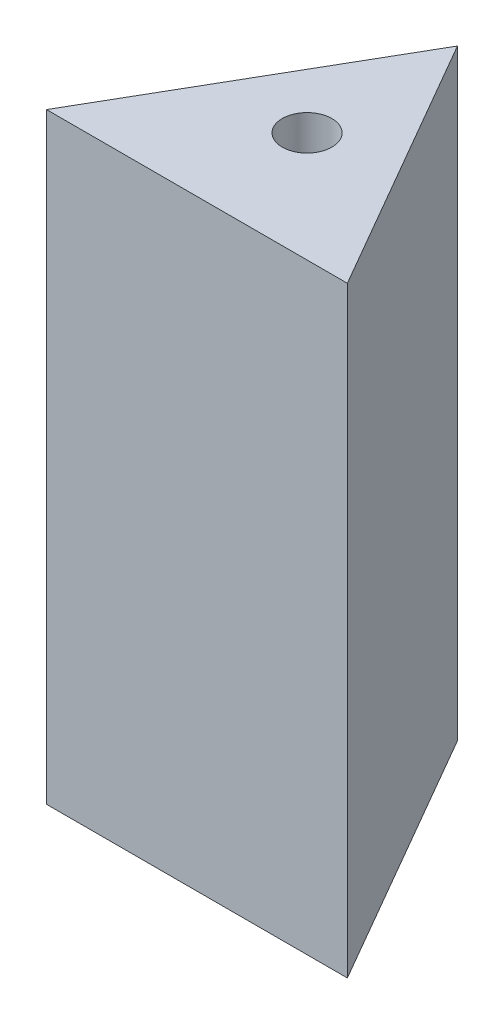
SolidWorks part; units mm, degrees
ref_plane "前视基准面" through (0, 0, 0) normal (0, 0, 1) x (1, 0, 0)
ref_plane "上视基准面" through (0, 0, 0) normal (0, 1, 0) x (1, 0, 0)
ref_plane "右视基准面" through (0, 0, 0) normal (1, 0, 0) x (0, 0, -1)
sketch "草图1" plane through (0, 0, 0) normal (0, 1, 0) x (1, 0, 0)
  line L0 (0, 0) -> (20, 0)
  line L1 (10, 17.3205) -> (20, 0)
  line L2 (0, 0) -> (10, 17.3205)
  line L3 (10, 17.3205) -> (10, 7.3205)
extrude "凸台-拉伸1" add sketch "草图1" along normal blind 40
sketch "草图5" plane through (0, 0, 0) normal (0, -1, 0) x (1, 0, 0)
  line L0 (10, -17.3205) -> (10, -7.3205)
hole_wizard "M4 螺纹孔1" positions "草图6" profile "草图7" tap size "M4" standard "GB"
sketch "草图6" plane through (0, 0, 0) normal (0, -1, 0) x (-1, 0, 0)
  point P0 (-10, 7.3205)
sketch "草图7" plane through (10, 0, -7.3205) normal (1, 0, 0) x (0, 0, -1)
  line L0 (0, 0) -> (0, 11.0914)
  line L1 (0, 11.0914) -> (1.65, 10.1)
  line L2 (1.65, 10.1) -> (1.65, 0)
  line L5 (1.65, 0) -> (0, 0)
  line L10 (0, 11.0914) -> (-1.65, 10.1) construction
  line L11 (0, -6.35) -> (0, 107.95) construction
  dimension "螺纹孔钻头直径" = 3.3
  dimension "螺纹孔钻头深度" = 10.1
  dimension "导头角度" = 118
cosmetic thread "孔螺蚊线1" parameters "D1"=8, "D2"=4
hole_wizard "M4 螺纹孔2" positions "草图8" profile "草图9" tap size "M4" standard "GB"
sketch "草图8" plane through (0, 40, 0) normal (0, 1, 0) x (1, 0, 0)
  point P0 (10, 7.3205)
sketch "草图9" plane through (10, 40, -7.3205) normal (1, 0, 0) x (0, 0, 1)
  line L0 (0, 0) -> (0, 11.0914)
  line L1 (0, 11.0914) -> (1.65, 10.1)
  line L2 (1.65, 10.1) -> (1.65, 0)
  line L5 (1.65, 0) -> (0, 0)
  line L10 (0, 11.0914) -> (-1.65, 10.1) construction
  line L11 (0, -6.35) -> (0, 107.95) construction
  dimension "螺纹孔钻头直径" = 3.3
  dimension "螺纹孔钻头深度" = 10.1
  dimension "导头角度" = 118
cosmetic thread "孔螺蚊线2" parameters "D1"=8, "D2"=4
sketch "草图10" plane through (0, 0, 0) normal (0, -1, 0) x (-1, 0, 0)
  line L0 (-10.1419, 13.0854) -> (-10.1064, 12.9436)
sketch "草图11" plane through (0, 0, 0) normal (-0.866, 0, -0.5) x (-0.5, 0, 0.866)
  line L0 (-10, 0) -> (-10, 5)
  line L1 (0, 0) -> (-20, 0) construction
  line L2 (-10, 5) -> (-10, 40)
  line L3 (0, 40) -> (-20, 40) construction
  line L4 (-10, 40) -> (-10, 35)
hole_wizard "M4 螺纹孔3" positions "草图14" profile "草图15" tap size "M4" standard "GB"
sketch "草图14" plane through (0, 0, 0) normal (-0.866, 0, -0.5) x (-0.5, 0, 0.866)
  point P0 (-10, 35)
  point P3 (-10, 5)
sketch "草图15" plane through (5, 35, -8.6603) normal (0, 1, 0) x (-0.5, 0, 0.866)
  line L0 (0, 0) -> (0, 11.0914)
  line L1 (0, 11.0914) -> (1.65, 10.1)
  line L2 (1.65, 10.1) -> (1.65, 0)
  line L5 (1.65, 0) -> (0, 0)
  line L10 (0, 11.0914) -> (-1.65, 10.1) construction
  line L11 (0, -6.35) -> (0, 107.95) construction
  dimension "螺纹孔钻头直径" = 3.3
  dimension "螺纹孔钻头深度" = 10.1
  dimension "导头角度" = 118
cosmetic thread "孔螺蚊线3" parameters "D1"=8, "D2"=4
cosmetic thread "孔螺蚊线4" parameters "D1"=8, "D2"=4
